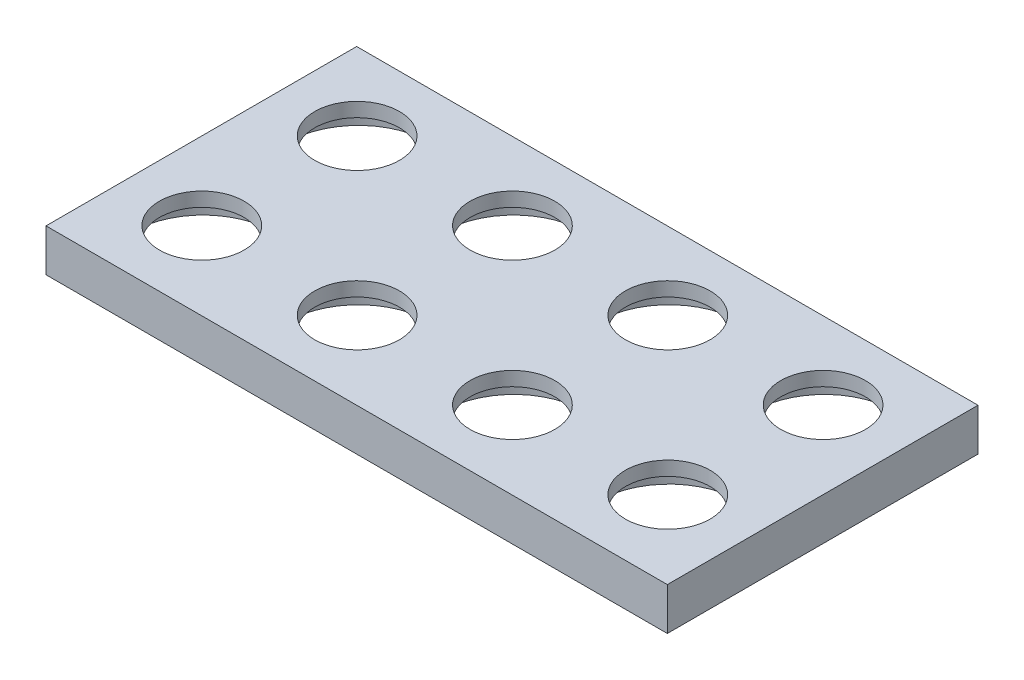
SolidWorks part; units mm, degrees
ref_plane "Front Plane" through (0, 0, 0) normal (0, 0, 1) x (1, 0, 0)
ref_plane "Top Plane" through (0, 0, 0) normal (0, 1, 0) x (1, 0, 0)
ref_plane "Right Plane" through (0, 0, 0) normal (1, 0, 0) x (0, 0, -1)
sketch "Sketch2" plane through (0, 0, 0) normal (0, 1, 0) x (1, 0, 0)
  line L1 (0, 0) -> (22, 0)
  line L2 (0, 0) -> (0, 22)
  line L3 (0, 22) -> (22, 22)
  line L4 (22, 0) -> (22, 22)
  dimension "D1" = 22
  dimension "D2" = 22
extrude "Boss-Extrude1" add sketch "Sketch2" against normal blind 6
sketch "Sketch3" plane through (0, 0, 0) normal (0, 1, 0) x (1, 0, 0)
  line L0 (22, 0) -> (22, 22) construction
  circle A0 centre (11, 11.0622) radius 6
  dimension "D1" = 12
  dimension "D2" = 11
extrude "Cut-Extrude1" cut sketch "Sketch3" against normal blind 2
sketch "Sketch4" plane through (0, -6, 0) normal (0, -1, 0) x (1, 0, 0)
  line L0 (22, 0) -> (22, -22) construction
  circle A0 centre (11, -11.2539) radius 10.175
  point P6 (8.862, -18.9349)
  dimension "D1" = 20.35
  dimension "D2" = 11
extrude "Cut-Extrude2" cut sketch "Sketch4" against normal blind 4
pattern_linear "LPattern1" count 4 spacing 22 along (-1, 0, 0) of "Boss-Extrude1", "Cut-Extrude2", "Cut-Extrude1"
pattern_linear "LPattern2" count 2 spacing 22 along (0, 0, -1) of "Boss-Extrude1", "Cut-Extrude2", "LPattern1", "Cut-Extrude1"
